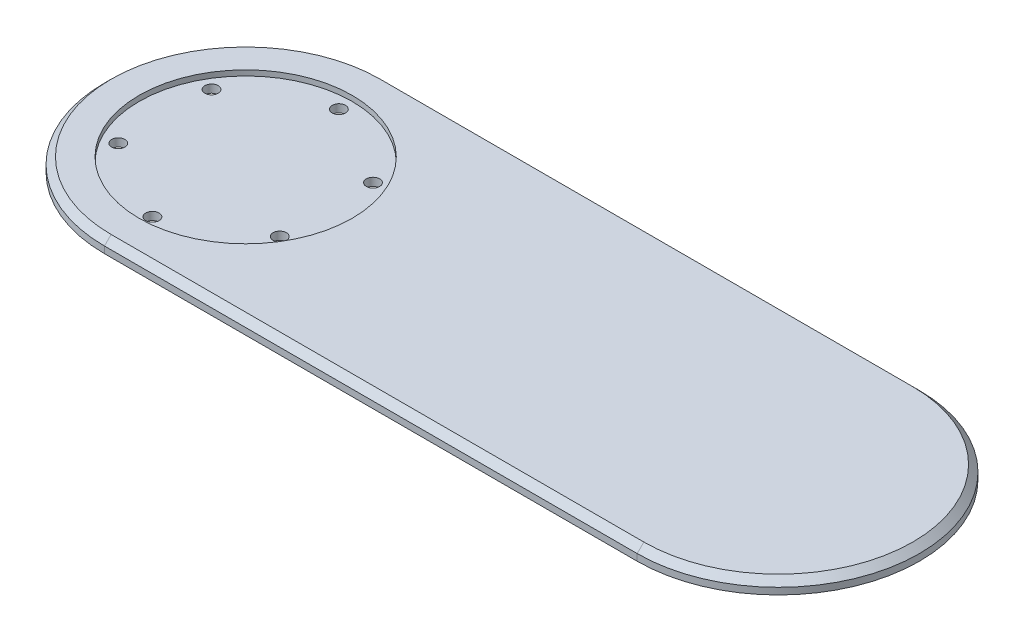
SolidWorks part; units mm, degrees
ref_plane "Front Plane" through (0, 0, 0) normal (0, 0, 1) x (1, 0, 0)
ref_plane "Top Plane" through (0, 0, 0) normal (0, 1, 0) x (1, 0, 0)
ref_plane "Right Plane" through (0, 0, 0) normal (1, 0, 0) x (0, 0, -1)
sketch "Sketch1" plane through (0, 0, 0) normal (0, 1, 0) x (1, 0, 0)
  line L0 (-100, 0) -> (-79.7951, 0) construction
  line L1 (-100, -53) -> (100, -53)
  line L2 (-100, -53) -> (-100, 53)
  line L3 (-100, 53) -> (100, 53)
  line L4 (100, -53) -> (100, 53)
  line L5 (-100, -53) -> (100, 53) construction
  line L6 (-100, 53) -> (100, -53) construction
  circle A0 centre (-100, 0) radius 53
  circle A1 centre (100, 0) radius 53
  circle A2 centre (-100, 0) radius 35 construction
  circle A3 centre (-100, 35) radius 2.5
  circle A4 centre (-69.6891, 17.5) radius 2.5
  circle A5 centre (-69.6891, -17.5) radius 2.5
  circle A6 centre (-100, -35) radius 2.5
  circle A7 centre (-130.3109, -17.5) radius 2.5
  circle A8 centre (-130.3109, 17.5) radius 2.5
  point P0 (0, 0)
  point P13 (0, 0)
  point P14 (0, 0)
  point P27 (-100, 0)
  dimension "D3" = 70
  dimension "D4" = 5
  dimension "D1" = 200
  dimension "D2" = 106
  dimension "D5" = 6
extrude "Boss-Extrude1" add sketch "Sketch1" along normal blind 5 contours L2 A0 | L2 A0 | A1 L3 A0 L1 | L4 A1 | L4 A1
sketch "Sketch2" plane through (0, 5, 0) normal (0, 1, 0) x (1, 0, 0)
  line L0 (-130.3109, 17.5) -> (-69.6891, -17.5) construction
  line L1 (-130.3109, -17.5) -> (-69.6891, 17.5) construction
  circle A0 centre (-100, 0) radius 40
  dimension "D1" = 80
extrude "Cut-Extrude1" cut sketch "Sketch2" against normal blind 2
chamfer "Chamfer1" distance 2.5 angle 45 4 edges at (153, 5, 0) (0, 5, -53) (-153, 5, 0) (0, 5, 53)
